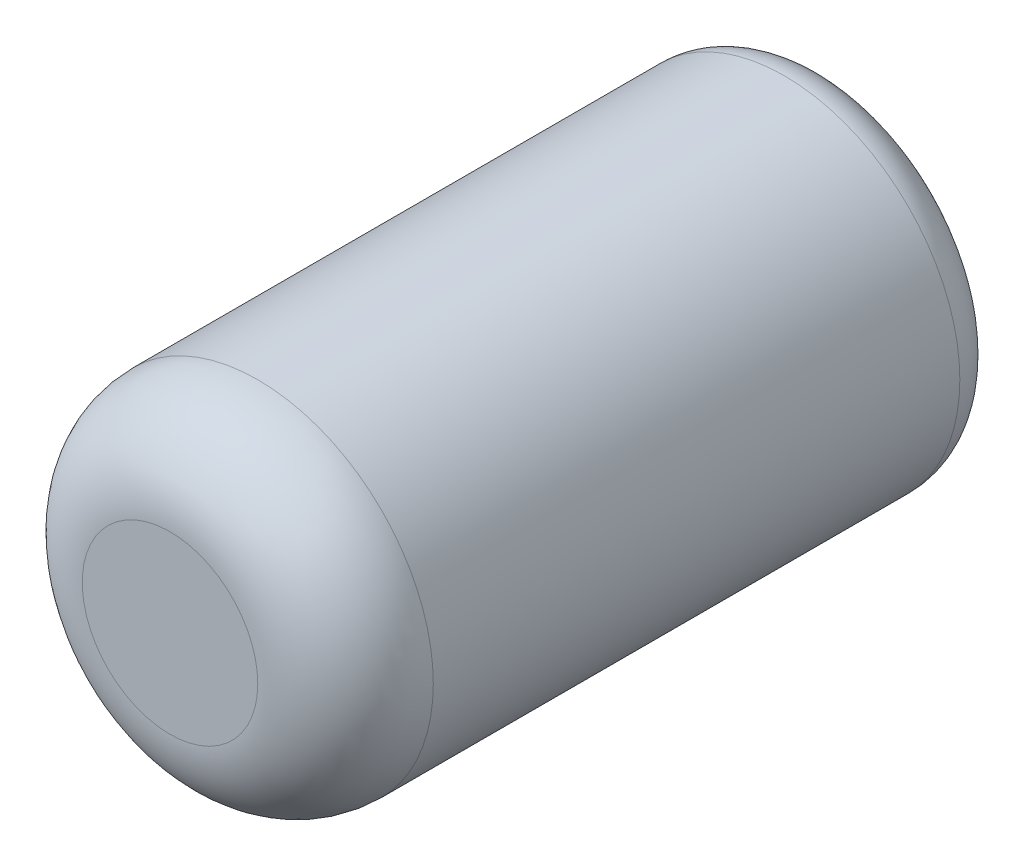
SolidWorks part; units mm, degrees
material "Messing"
ref_plane "Ebene vorne" through (0, 0, 0) normal (0, 0, 1) x (1, 0, 0)
ref_plane "Ebene oben" through (0, 0, 0) normal (0, 1, 0) x (1, 0, 0)
ref_plane "Ebene rechts" through (0, 0, 0) normal (1, 0, 0) x (0, 0, -1)
sketch "Skizze1" plane through (0, 0, 0) normal (0, 0, 1) x (1, 0, 0)
  circle A0 centre (0, 0) radius 4
  dimension "D1" = 8
extrude "Aufsatz-Linear austragen1" add sketch "Skizze1" along normal blind 15
cosmetic thread "Gewindedarstellung1" parameters "D1"=10, "D2"=6.619
fillet "Verrundung1" radius 2 1 edges at (4, 0, 15)
fillet "Verrundung2" radius 1 1 edges at (4, 0, 0)
